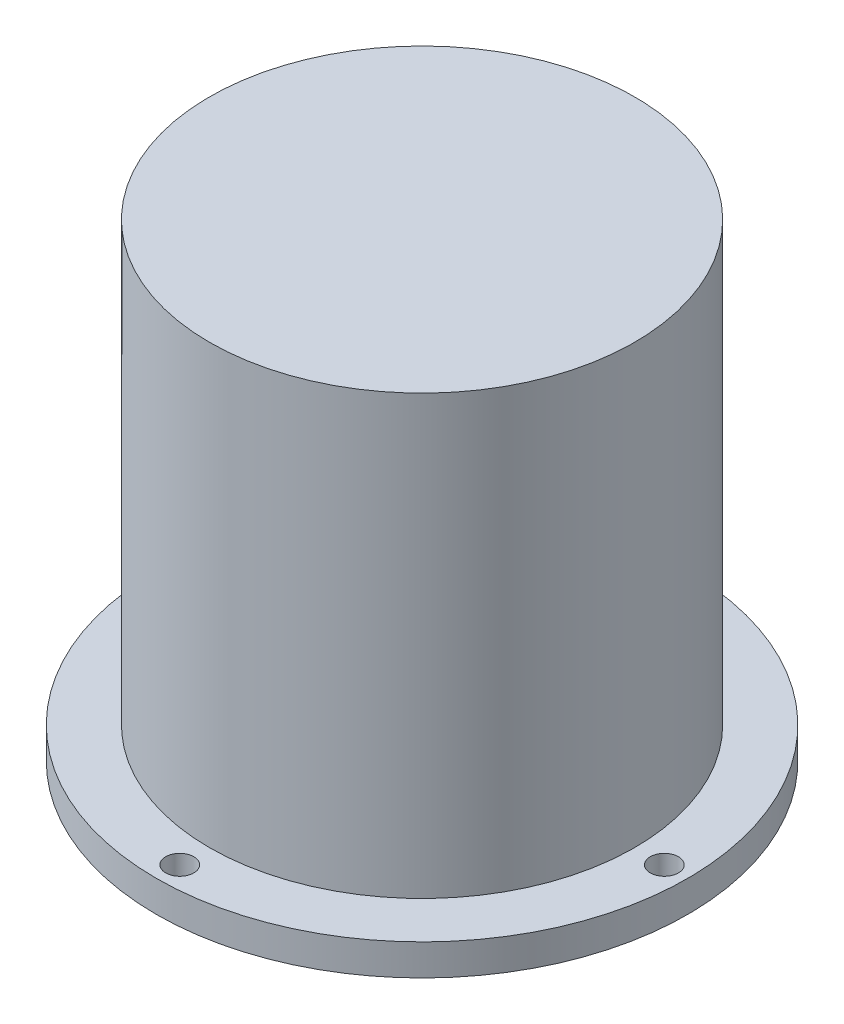
SolidWorks part; units mm, degrees
ref_plane "Plan de face" through (0, 0, 0) normal (0, 0, 1) x (1, 0, 0)
ref_plane "Plan de dessus" through (0, 0, 0) normal (0, 1, 0) x (1, 0, 0)
ref_plane "Plan de droite" through (0, 0, 0) normal (1, 0, 0) x (0, 0, -1)
sketch "Esquisse1" plane through (0, 0, 0) normal (0, 1, 0) x (1, 0, 0)
  circle A0 centre (0, 0) radius 42.5
  dimension "D1" = 85
extrude "Boss.-Extru.2" add sketch "Esquisse1" along normal blind 5 contours A0
sketch "Esquisse12" plane through (0, 5, 0) normal (0, 1, 0) x (1, 0, 0)
  line L0 (0, 42.5) -> (0, -42.5)
  line L1 (-42.5, 0) -> (42.5, 0)
  circle A0 centre (0, 0) radius 38.75
  circle A1 centre (0, 0) radius 42.5 construction
  circle A2 centre (0, 0) radius 34
  point P10 (0, 38.75)
  point P11 (38.75, 0)
  point P12 (0, -38.75)
  point P13 (-38.75, 0)
  dimension "D1" = 77.5
  dimension "D2" = 68
hole_wizard "Dégagement M42" positions "Esquisse3D3" profile "Esquisse13" hole size "M4" standard "ISO" end condition through all
sketch3d "Esquisse3D3"
  point P0 (0, 5, -38.75)
  point P3 (-38.75, 5, 0)
  point P6 (0, 5, 38.75)
  point P9 (38.75, 5, 0)
sketch "Esquisse13" plane through (0, 5, -38.75) normal (1, 0, 0) x (0, 0, 1)
  line L0 (0, 0) -> (0, 5)
  line L1 (0, 5) -> (2.25, 5)
  line L2 (2.25, 5) -> (2.25, 0)
  line L5 (2.25, 0) -> (0, 0)
  line L11 (0, -6.35) -> (0, 107.95) construction
  dimension "Diamètre du perçage jusqu'au prochain" = 4.5
  dimension "Profondeur du perçage jusqu'au prochain" = 5
extrude "Boss.-Extru.3" add sketch "Esquisse12" along normal blind 70 contours A2
